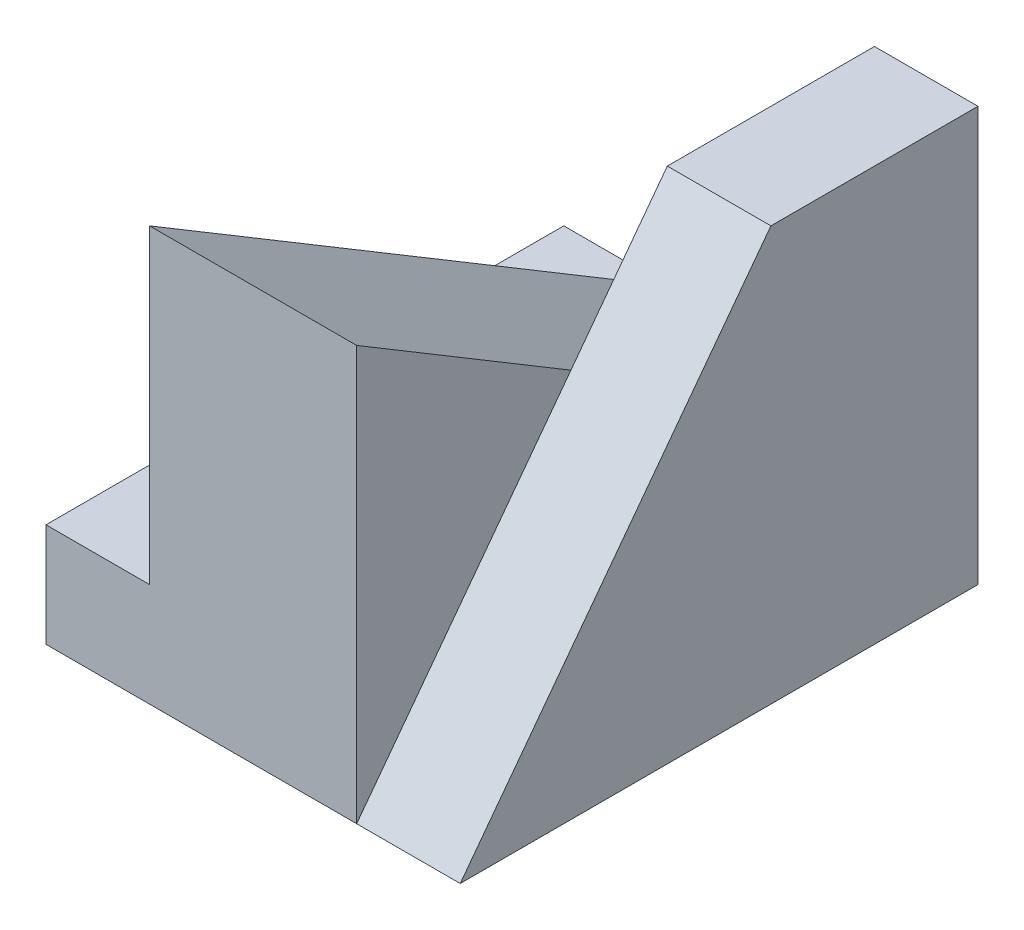
SolidWorks part; units mm, degrees
ref_plane "Front Plane" through (0, 0, 0) normal (0, 0, 1) x (1, 0, 0)
ref_plane "Top Plane" through (0, 0, 0) normal (0, 1, 0) x (1, 0, 0)
ref_plane "Right Plane" through (0, 0, 0) normal (1, 0, 0) x (0, 0, -1)
sketch "Sketch1" plane through (0, 0, 0) normal (1, 0, 0) x (0, 0, -1)
  line L0 (0, 0) -> (0, 4)
  line L1 (0, 4) -> (-2, 4)
  line L2 (-2, 4) -> (-5, 0)
  line L3 (-5, 0) -> (0, 0)
  dimension "D1" = 2
  dimension "D2" = 4
  dimension "D3" = 5
extrude "Boss-Extrude1" add sketch "Sketch1" along normal blind 1
sketch "Sketch2" plane through (0, 0, 0) normal (-1, 0, 0) x (0, 0, 1)
  line L0 (0, 0) -> (5, 0)
  line L1 (5, 0) -> (5, 4)
  line L2 (5, 4) -> (0, 1)
  line L3 (0, 0) -> (0, 4) construction
  line L4 (0, 1) -> (0, 0)
  dimension "D1" = 1
  dimension "D2" = 4
extrude "Boss-Extrude2" add sketch "Sketch2" along normal blind 2
sketch "Sketch3" plane through (-2, 0, 0) normal (-1, 0, 0) x (0, 0, 1)
  line L1 (0, 1) -> (5, 1)
  line L2 (0, 1) -> (0, 0)
  line L3 (0, 0) -> (5, 0)
  line L4 (5, 1) -> (5, 0)
extrude "Boss-Extrude3" add sketch "Sketch3" along normal blind 1
